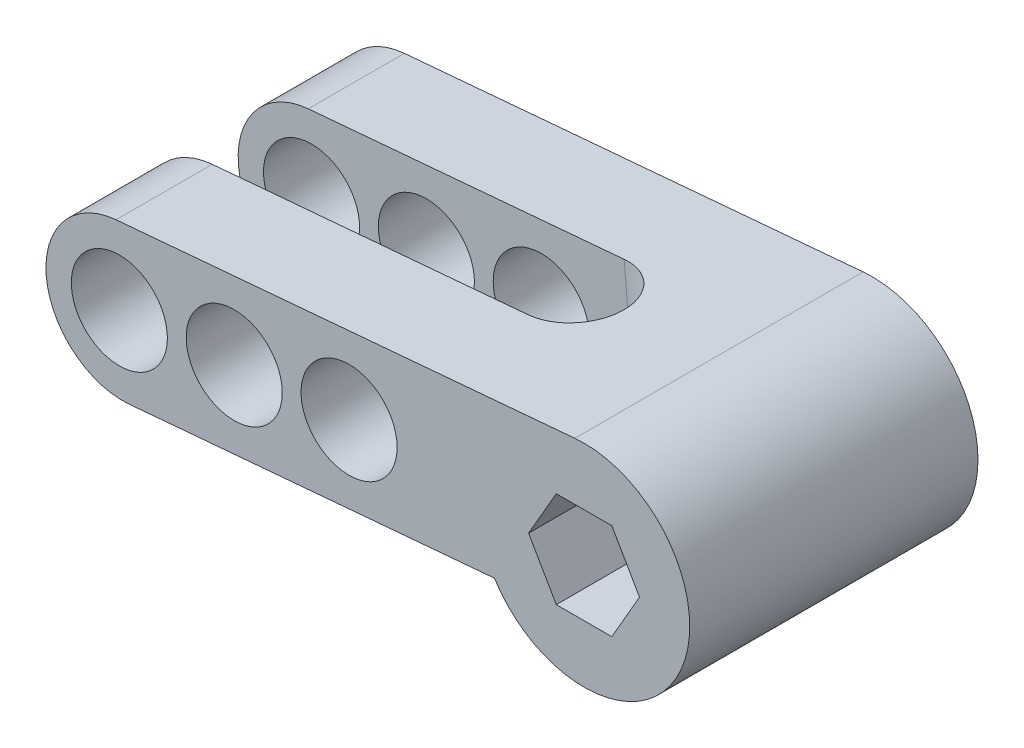
SolidWorks part; units mm, degrees
ref_plane "Front Plane" through (0, 0, 0) normal (0, 0, 1) x (1, 0, 0)
ref_plane "Top Plane" through (0, 0, 0) normal (0, 1, 0) x (1, 0, 0)
ref_plane "Right Plane" through (0, 0, 0) normal (1, 0, 0) x (0, 0, -1)
sketch "Sketch1" plane through (0, 0, 0) normal (0, 0, 1) x (1, 0, 0)
  line L0 (27.0054, -4.7977) -> (29.8922, 0.2023)
  line L1 (29.8922, 0.2023) -> (27.0054, 5.2023)
  line L2 (27.0054, 5.2023) -> (21.2319, 5.2023)
  line L3 (21.2319, 5.2023) -> (18.3452, 0.2023)
  line L4 (18.3452, 0.2023) -> (21.2319, -4.7977)
  line L5 (21.2319, -4.7977) -> (27.0054, -4.7977)
  line L6 (23.16, 11.1605) -> (-24.5786, 6.9839)
  line L7 (-23.1841, -8.9552) -> (14.7938, -5.6326)
  line L10 (24.1187, 0.2023) -> (-12.9799, 0.2023) construction
  circle A0 centre (24.1187, 0.2023) radius 5 construction
  arc A2 (-24.5786, 6.9839) -> (-23.1841, -8.9552) centre (-23.8813, -0.9857) ccw
  arc A3 (14.7938, -5.6326) -> (23.16, 11.1605) centre (24.1187, 0.2023) ccw
  point P16 (0, 0)
  point P17 (0, 0)
  dimension "D4" = 8
  dimension "D2" = 5
  dimension "D3" = 48
extrude "Boss-Extrude1" add sketch "Sketch1" along normal blind 30
sketch "Sketch2" plane through (-0.7931, 9.0649, 0) normal (-0.0872, 0.9962, 0) x (0.9962, 0.0872, 0)
  line L0 (24.0445, 0) -> (-23.8764, 0) construction
  line L1 (-32.8812, -10) -> (9.1188, -10)
  line L2 (-32.8812, -10) -> (-32.8812, -20)
  line L3 (-32.8812, -20) -> (9.1188, -20)
  arc A0 (9.1188, -20) -> (9.1188, -10) centre (9.1188, -15) ccw
  dimension "D1" = 10
  dimension "D2" = 42
  dimension "D3" = 10
extrude "Cut-Extrude1" cut sketch "Sketch2" against normal through all
sketch "Sketch3" plane through (0, 0, 30) normal (0, 0, 1) x (1, 0, 0)
  line L0 (23.16, 11.1605) -> (-24.5786, 6.9839) construction
  circle A0 centre (-24.2435, -1.0174) radius 5
  circle A1 centre (-12.2892, 0.0285) radius 5
  circle A2 centre (-0.3349, 1.0744) radius 5
  circle A4 centre (11.6195, 2.1203) radius 5 [skipped]
  dimension "D1" = 10
  dimension "D2" = 4
  dimension "D3" = 8
extrude "Cut-Extrude2" cut sketch "Sketch3" against normal through all
